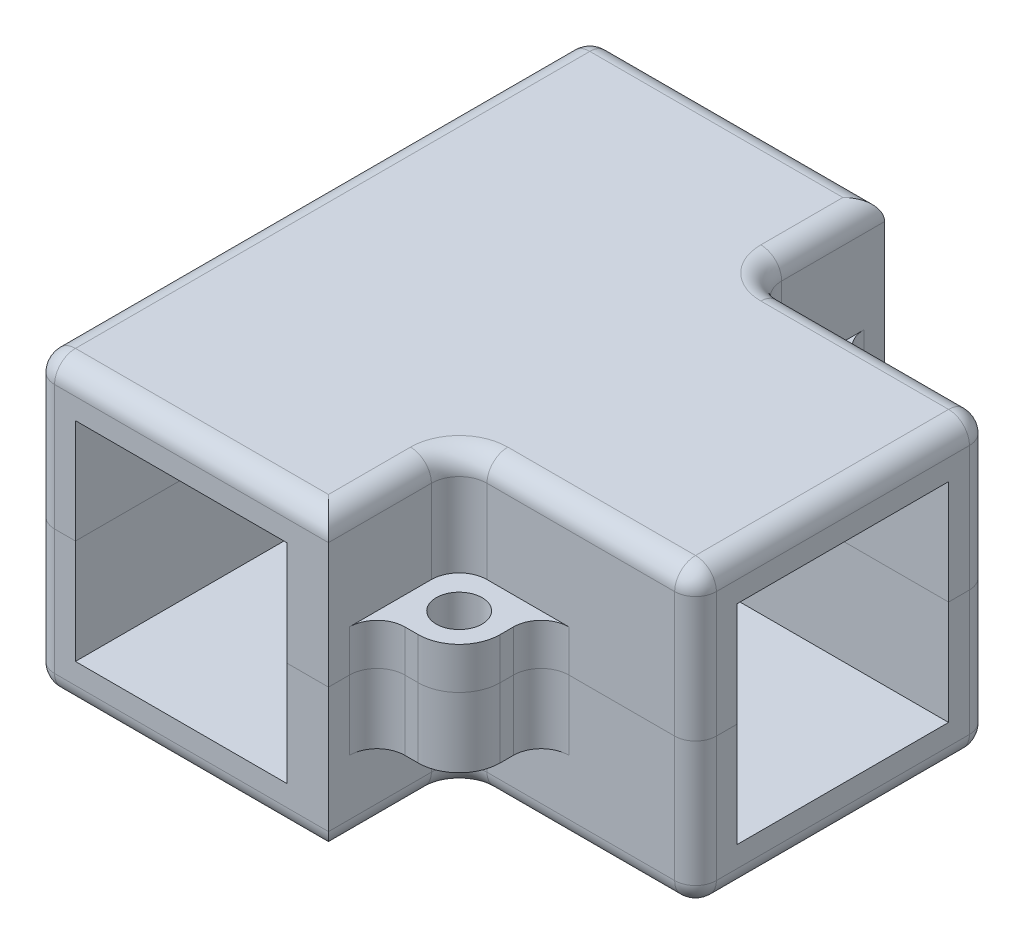
SolidWorks part; units mm, degrees
ref_plane "Front Plane" through (0, 0, 0) normal (0, 0, 1) x (1, 0, 0)
ref_plane "Top Plane" through (0, 0, 0) normal (0, 1, 0) x (1, 0, 0)
ref_plane "Right Plane" through (0, 0, 0) normal (1, 0, 0) x (0, 0, -1)
sketch "Sketch1" plane through (0, 0, 0) normal (0, 1, 0) x (1, 0, 0)
  line L0 (15.2, 20) -> (35.2, 20) construction
  line L1 (0, 0) -> (15.2, 0)
  line L2 (0, 0) -> (0, 40)
  line L3 (0, 40) -> (15.2, 40)
  line L4 (15.2, 0) -> (15.2, 40)
  line L6 (15.2, 12.4) -> (35.2, 12.4)
  line L7 (15.2, 12.4) -> (15.2, 27.6)
  line L8 (15.2, 27.6) -> (35.2, 27.6)
  line L9 (35.2, 12.4) -> (35.2, 27.6)
  line L10 (15.2, 12.4) -> (35.2, 27.6) construction
  line L11 (15.2, 27.6) -> (35.2, 12.4) construction
  point P7 (25.2, 20)
  dimension "D1" = 15.2
  dimension "D2" = 15.2
  dimension "D3" = 40
  dimension "D4" = 20
sketch "Sketch3" plane through (0, 0, 0) normal (0, 1, 0) x (1, 0, 0)
  line L0 (35.2, 27.6) -> (15.2, 27.6)
  line L1 (15.2, 27.6) -> (15.2, 40)
  line L2 (15.2, 40) -> (18.2, 40)
  line L3 (18.2, 40) -> (18.2, 30.6)
  line L4 (18.2, 30.6) -> (35.2, 30.6)
  line L5 (35.2, 30.6) -> (35.2, 27.6)
  line L6 (0, 20) -> (35.2, 20) construction
  line L7 (0, 0) -> (0, 40) construction
  line L8 (18.2, 9.4) -> (35.2, 9.4)
  line L9 (18.2, 0) -> (18.2, 9.4)
  line L10 (15.2, 0) -> (18.2, 0)
  line L11 (15.2, 12.4) -> (15.2, 0)
  line L12 (35.2, 12.4) -> (15.2, 12.4)
  line L13 (35.2, 9.4) -> (35.2, 12.4)
  line L15 (0, 40) -> (-3, 40)
  line L16 (0, 40) -> (0, 0)
  line L17 (0, 0) -> (-3, 0)
  line L18 (-3, 40) -> (-3, 0)
  dimension "D1" = 3
extrude "Boss-Extrude1" add sketch "Sketch3" along normal blind 7.5
sketch "Sketch4" plane through (0, 7.5, 0) normal (0, 1, 0) x (1, 0, 0)
  line L0 (-3, 40) -> (-3, 0)
  line L1 (-3, 0) -> (18.2, 0)
  line L2 (18.2, 0) -> (18.2, 9.4)
  line L3 (18.2, 9.4) -> (35.2, 9.4)
  line L4 (35.2, 9.4) -> (35.2, 30.6)
  line L5 (35.2, 30.6) -> (18.2, 30.6)
  line L6 (18.2, 30.6) -> (18.2, 40)
  line L7 (18.2, 40) -> (-3, 40)
extrude "Boss-Extrude2" add sketch "Sketch4" along normal blind 3
sketch "Sketch5" plane through (0, 0, 0) normal (0, 1, 0) x (1, 0, 0)
  line L0 (18.2, 30.6) -> (18.2, 40) construction
  line L1 (35.2, 30.6) -> (18.2, 30.6) construction
  line L4 (21.15, 36.5) -> (18.2, 36.5)
  line L5 (18.2, 36.5) -> (18.2, 30.6)
  line L6 (18.2, 30.6) -> (24.1, 30.6)
  line L7 (24.1, 30.6) -> (24.1, 33.55)
  line L8 (35.2, 20) -> (-3, 20) construction
  line L9 (35.2, 9.4) -> (35.2, 30.6) construction
  line L10 (-3, 40) -> (-3, 0) construction
  line L11 (24.1, 9.4) -> (24.1, 6.45)
  line L12 (18.2, 9.4) -> (24.1, 9.4)
  line L13 (18.2, 3.5) -> (18.2, 9.4)
  line L14 (21.15, 3.5) -> (18.2, 3.5)
  line L15 (-5.95, 22.95) -> (-3, 22.95)
  line L16 (-3, 22.95) -> (-3, 17.05)
  line L17 (-3, 17.05) -> (-5.95, 17.05)
  circle A0 centre (21.15, 33.55) radius 1.65
  circle A2 centre (21.15, 33.55) radius 2.95 construction
  arc A4 (24.1, 33.55) -> (21.15, 36.5) centre (21.15, 33.55) ccw
  circle A5 centre (21.15, 6.45) radius 2.95 construction
  arc A6 (24.1, 6.45) -> (21.15, 3.5) centre (21.15, 6.45) cw
  circle A7 centre (21.15, 6.45) radius 1.65
  circle A8 centre (-5.95, 20) radius 2.95 construction
  circle A9 centre (-5.95, 20) radius 1.65
  arc A10 (-5.95, 17.05) -> (-5.95, 22.95) centre (-5.95, 20) cw
  dimension "D1" = 3.3
  dimension "D2" = 5.9
  dimension "D3" = 5.9
  dimension "D4" = 3.3
extrude "Boss-Extrude3" add sketch "Sketch5" along normal blind 3
fillet "Fillet1" radius 2 2 edges at (18.2, 6.75, -9.4) (18.2, 6.75, -30.6)
fillet "Fillet2" radius 2 6 edges at (18.2, 1.5, -3.5) (24.1, 1.5, -9.4) (24.1, 1.5, -30.6) (18.2, 1.5, -36.5) (-3, 1.5, -22.95) (-3, 1.5, -17.05)
fillet "Fillet3" radius 1.5 14 edges at (18.2, 10.5, -36.3) (18.7858, 10.5, -31.1858) (27.7, 10.5, -30.6) (35.2, 10.5, -20) (27.7, 10.5, -9.4) (18.7858, 10.5, -8.8142) (18.2, 10.5, -3.7) (7.6, 10.5, 0) (-3, 10.5, -20) (7.6, 10.5, -40) (-3, 5.25, -40) (-3, 5.25, 0) (35.2, 5.25, -30.6) (35.2, 5.25, -9.4)
mirror "Mirror1" about plane through (0, 0, 0) normal (0, -1, 0) of bodies 105
sketch "Sketch6" plane through (0, 0, 0) normal (0, 1, 0) x (1, 0, 0)
  circle A0 centre (21.15, 6.45) radius 1.65 construction
  circle A1 centre (21.15, 33.55) radius 1.65 construction
  circle A2 centre (-5.95, 20) radius 1.65 construction
  circle A3 centre (21.15, 6.45) radius 1.65
  circle A4 centre (21.15, 33.55) radius 1.65
  circle A5 centre (-5.95, 20) radius 1.65
extrude "Boss-Extrude4" add sketch "Sketch6" against normal up to vertex
other "Move Face1" face at (21.4523, -3, -33.8523) face at (21.4523, -3, -6.1477) face at (-5.0036, -3, -20) parameters "D1"=2
sketch "Sketch7" plane through (0, 0, 0) normal (0, 1, 0) x (1, 0, 0)
  circle A0 centre (-5.95, 20) radius 2.1
  circle A1 centre (21.15, 33.55) radius 2.1
  circle A2 centre (21.15, 6.45) radius 2.1
  dimension "D1" = 4.2
extrude "Cut-Extrude1" cut sketch "Sketch7" against normal blind 3
